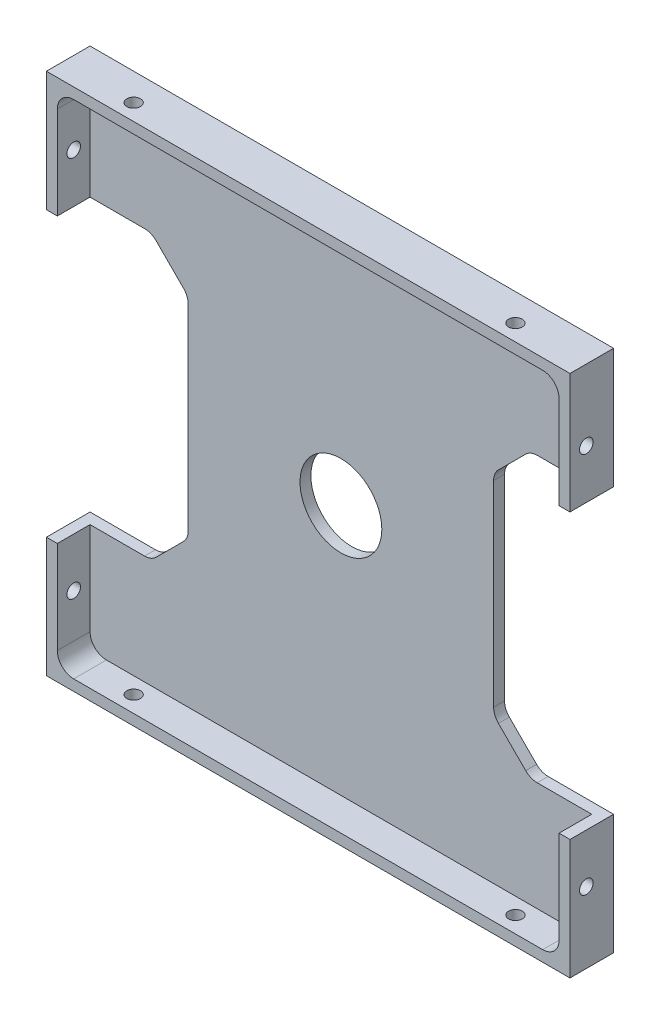
SolidWorks part; units mm, degrees
material "6061-T6 (SS)"
ref_plane "Front" through (0, 0, 0) normal (0, 0, 1) x (1, 0, 0)
ref_plane "Top" through (0, 0, 0) normal (0, 1, 0) x (1, 0, 0)
ref_plane "Right" through (0, 0, 0) normal (1, 0, 0) x (0, 0, -1)
sketch "Sketch1" plane through (0, 0, 0) normal (0, 0, 1) x (1, 0, 0)
  line L1 (-48, -48) -> (48, -48)
  line L2 (-48, -48) -> (-48, 48)
  line L3 (-48, 48) -> (48, 48)
  line L4 (48, -48) -> (48, 48)
  line L5 (-48, -48) -> (48, 48) construction
  line L6 (-48, 48) -> (48, -48) construction
  point P0 (0, 0)
  dimension "D1" = 96
  dimension "D2" = 96
extrude "Boss-Extrude1" add sketch "Sketch1" along normal blind 8
sketch "Sketch2" plane through (0, 0, 8) normal (0, 0, 1) x (1, 0, 0)
  line L1 (46, -46) -> (-46, -46)
  line L2 (46, -46) -> (46, 46)
  line L3 (46, 46) -> (-46, 46)
  line L4 (-46, -46) -> (-46, 46)
  line L5 (46, -46) -> (-46, 46) construction
  line L6 (46, 46) -> (-46, -46) construction
  point P0 (0, 0)
  dimension "D1" = 92
  dimension "D2" = 92
extrude "Component Platform" cut sketch "Sketch2" against normal blind 6
sketch "Sketch3" plane through (0, 0, 2) normal (0, 0, 1) x (1, 0, 0)
  line L1 (-33.8787, -25.1213) -> (-28.8787, -20.1213)
  line L2 (-33.8787, 25.1213) -> (-28.8787, 20.1213)
  line L3 (-28, -18) -> (-28, 18)
  line L4 (-48, -26) -> (-36, -26)
  line L7 (-48, 48) -> (-48, -48) construction
  line L8 (0, -56.7987) -> (0, 73.4321) construction
  line L9 (46, -46) -> (-57.8147, 57.8147) construction
  line L18 (46, 46) -> (-68.5705, -68.5705) construction
  line L23 (-48, 26) -> (-36, 26)
  line L26 (-48, -26) -> (-48, 26)
  line L28 (-48, -48) -> (48, -48) construction
  line L29 (48, -26) -> (48, 26)
  line L30 (48, 26) -> (36, 26)
  line L31 (33.8787, 25.1213) -> (28.8787, 20.1213)
  line L32 (28, -18) -> (28, 18)
  line L33 (33.8787, -25.1213) -> (28.8787, -20.1213)
  line L34 (48, -26) -> (36, -26)
  arc A3 (-28.8787, -20.1213) -> (-28, -18) centre (-31, -18) ccw
  arc A4 (-28.8787, 20.1213) -> (-28, 18) centre (-31, 18) cw
  arc A13 (-33.8787, -25.1213) -> (-36, -26) centre (-36, -23) cw
  arc A15 (-33.8787, 25.1213) -> (-36, 26) centre (-36, 23) ccw
  arc A17 (33.8787, 25.1213) -> (36, 26) centre (36, 23) cw
  arc A18 (28.8787, 20.1213) -> (28, 18) centre (31, 18) ccw
  arc A19 (28.8787, -20.1213) -> (28, -18) centre (31, -18) cw
  arc A20 (33.8787, -25.1213) -> (36, -26) centre (36, -23) ccw
  point P0 (-48, 0)
  point P37 (-48, 0)
  dimension "D2" = 3
  dimension "D3" = 3
  dimension "D4" = 20
  dimension "D6" = 3
  dimension "D7" = 3
  dimension "D8" = 135
  dimension "D5" = 52
  dimension "D9" = 135
  dimension "D10" = 12
  dimension "D11" = 12
  dimension "D12" = 48
extrude "Cable Slots" cut sketch "Sketch3" against normal mid plane 12
sketch "Sketch4" plane through (0, 0, 2) normal (0, 0, 1) x (1, 0, 0)
  circle A0 centre (0, 0) radius 7.5
  dimension "D1" = 15
extrude "Center Mass Cut" cut sketch "Sketch4" against normal blind 6
ref_plane "Center Y-Plane" through (0, 0, 0) normal (1, 0, 0) x (0, 0, -1)
ref_plane "Center X-Plane" through (0, 0, 0) normal (0, -1, 0) x (-1, 0, 0)
fillet "Inner Corner Fillets" radius 3 4 edges at (46, -46, 5) (-46, -46, 5) (46, 46, 5) (-46, 46, 5)
sketch "Sketch8" plane through (48, 0, 0) normal (1, 0, 0) x (0, 0, -1)
  line L0 (-5, -48) -> (-5, 48) construction
  line L1 (-8, -48) -> (0, -48) construction
  line L2 (-8, 48) -> (0, 48) construction
  line L3 (-8, -48) -> (-8, -26) construction
  dimension "D1" = 3
hole_wizard "M3x0.5 Tapped Hole1" positions "Sketch9" profile "Sketch10" tap size "M3x0.5" standard "ANSI Metric"
sketch "Sketch9" plane through (48, 0, 0) normal (1, 0, 0) x (0, 0, -1)
  line L0 (-5, -48) -> (-5, 48) construction
  point P0 (-5, -35)
  point P4 (-5, 35)
  dimension "D1" = 70
  dimension "D2" = 35
sketch "Sketch10" plane through (48, -35, 5) normal (0, 1, 0) x (0, 0, -1)
  line L0 (0, 0) -> (0, 10.7511)
  line L1 (0, 10.7511) -> (1.25, 10)
  line L2 (1.25, 10) -> (1.25, 0)
  line L5 (1.25, 0) -> (0, 0)
  line L10 (0, 10.7511) -> (-1.25, 10) construction
  line L11 (0, -6.35) -> (0, 107.95) construction
  dimension "Tap Drill Dia." = 2.5
  dimension "Tap Drill Depth" = 10
  dimension "Drill Angle" = 118
sketch "Sketch11" plane through (0, -48, 0) normal (0, -1, 0) x (-1, 0, 0)
  line L0 (48, -5) -> (-48.0639, -5) construction
  line L1 (48, -8) -> (48, 0) construction
  line L2 (48, -8) -> (-48, -8) construction
  dimension "D1" = 3
hole_wizard "M3x0.5 Tapped Hole2" positions "Sketch12" profile "Sketch13" tap size "M3x0.5" standard "ANSI Metric"
sketch "Sketch12" plane through (0, -48, 0) normal (0, -1, 0) x (-1, 0, 0)
  line L0 (48, -5) -> (-48.0639, -5) construction
  point P0 (35, -5)
  point P4 (-35, -5)
  dimension "D1" = 70
  dimension "D2" = 35
sketch "Sketch13" plane through (-35, -48, 5) normal (1, 0, 0) x (0, 0, -1)
  line L0 (0, 0) -> (0, 10.7511)
  line L1 (0, 10.7511) -> (1.25, 10)
  line L2 (1.25, 10) -> (1.25, 0)
  line L5 (1.25, 0) -> (0, 0)
  line L10 (0, 10.7511) -> (-1.25, 10) construction
  line L11 (0, -6.35) -> (0, 107.95) construction
  dimension "Tap Drill Dia." = 2.5
  dimension "Tap Drill Depth" = 10
  dimension "Drill Angle" = 118
mirror "Mirror1" about plane through (0, 0, 0) normal (1, 0, 0) of "M3x0.5 Tapped Hole1"
mirror "Mirror2" about plane through (0, 0, 0) normal (0, -1, 0) of "M3x0.5 Tapped Hole2"
